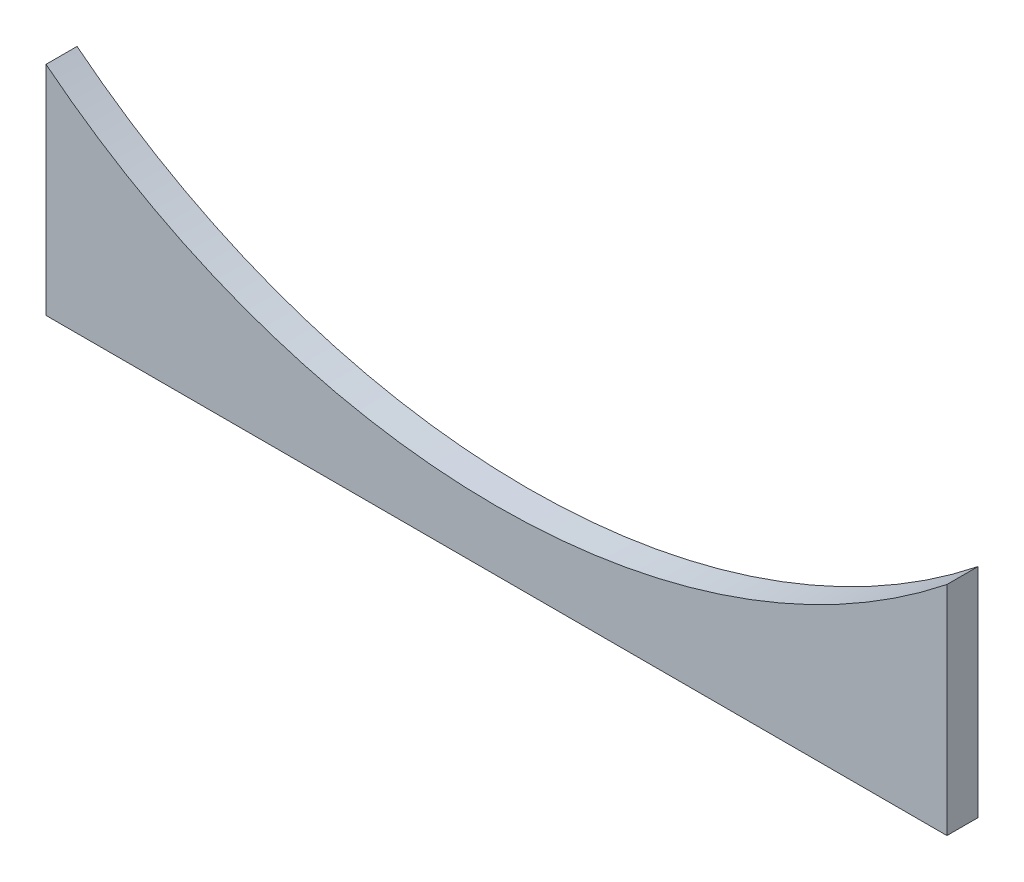
SolidWorks part; units mm, degrees
ref_plane "Front Plane" through (0, 0, 0) normal (0, 0, 1) x (1, 0, 0)
ref_plane "Top Plane" through (0, 0, 0) normal (0, 1, 0) x (1, 0, 0)
ref_plane "Right Plane" through (0, 0, 0) normal (1, 0, 0) x (0, 0, -1)
sketch "Sketch1" plane through (0, 0, 0) normal (0, 0, 1) x (1, 0, 0)
  line L1 (92.075, -22.225) -> (-92.075, -22.225)
  line L2 (92.075, -22.225) -> (92.075, 22.225)
  line L3 (92.075, 22.225) -> (-92.075, 22.225)
  line L4 (-92.075, -22.225) -> (-92.075, 22.225)
  line L5 (92.075, -22.225) -> (-92.075, 22.225) construction
  line L6 (92.075, 22.225) -> (-92.075, -22.225) construction
  point P0 (0, 0)
  dimension "D1" = 184.15
  dimension "D2" = 44.45
extrude "Boss-Extrude1" add sketch "Sketch1" along normal blind 6.35
sketch "Sketch2" plane through (0, 0, 6.35) normal (0, 0, 1) x (1, 0, 0)
  arc A0 (-92.075, 22.225) -> (92.075, 22.225) centre (0, 137.9433) ccw
extrude "Cut-Extrude1" cut sketch "Sketch2" against normal through all and the other way through all
